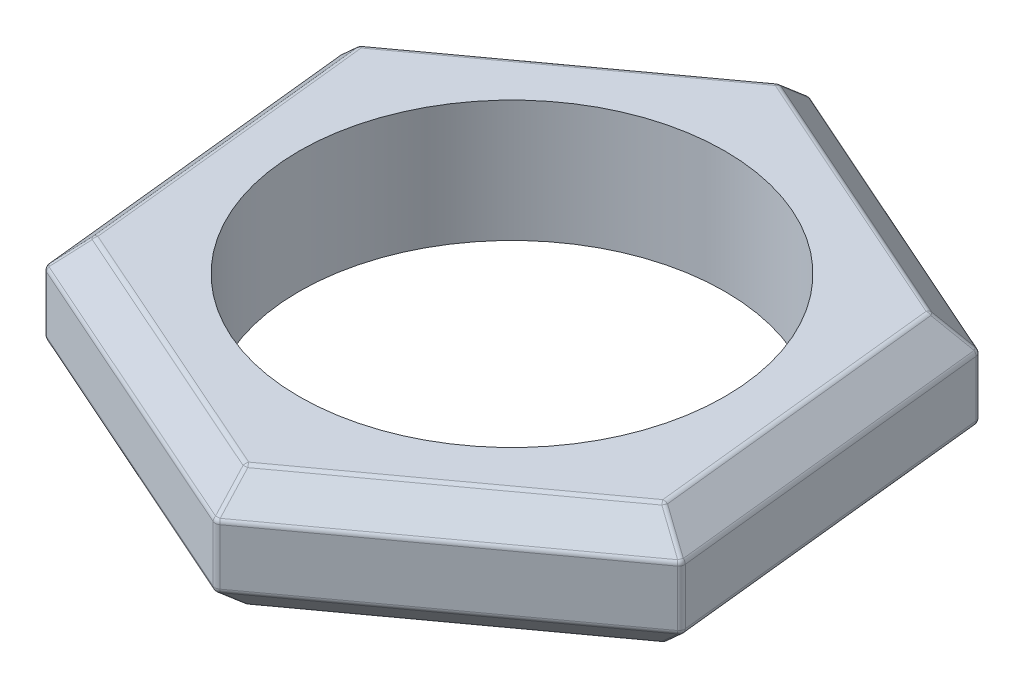
SolidWorks part; units mm, degrees
ref_plane "Front" through (0, 0, 0) normal (0, 0, 1) x (1, 0, 0)
ref_plane "Top" through (0, 0, 0) normal (0, 1, 0) x (1, 0, 0)
ref_plane "Right" through (0, 0, 0) normal (1, 0, 0) x (0, 0, -1)
sketch "Sketch1" plane through (0, 0, 0) normal (0, 1, 0) x (1, 0, 0)
  line L1 (5.028, -2.2293) -> (4.4446, 3.2397)
  line L2 (4.4446, 3.2397) -> (-0.5834, 5.469)
  line L3 (-0.5834, 5.469) -> (-5.028, 2.2293)
  line L4 (-5.028, 2.2293) -> (-4.4446, -3.2397)
  line L5 (-4.4446, -3.2397) -> (0.5834, -5.469)
  line L6 (0.5834, -5.469) -> (5.028, -2.2293)
  circle A0 centre (0, 0) radius 3.5
extrude "Extrude1" add sketch "Sketch1" along normal blind 2
chamfer "Chamfer1" distance 0.5 angle 45 6 edges at (-1.9306, 2, 4.3543) (-4.7363, 2, 0.5052) (-2.8057, 2, -3.8491) (1.9306, 2, -4.3543) (4.7363, 2, -0.5052) (2.8057, 2, 3.8491)
chamfer "Chamfer2" distance 0.5 angle 45 6 edges at (-4.7363, 0, 0.5052) (-2.8057, 0, -3.8491) (1.9306, 0, -4.3543) (4.7363, 0, -0.5052) (2.8057, 0, 3.8491) (-1.9306, 0, 4.3543)
fillet "Fillet1" radius 0.1 42 edges at (2.5111, 2, 3.4451) (2.8057, 1.5, 3.8491) (0.5834, 1, 5.469) (0.5527, 1.75, 5.1819) (-1.728, 2, 3.8972) (-1.9306, 1.5, 4.3543) (-4.4446, 1, 3.2397) (-4.2113, 1.75, 3.0697) (-4.7363, 1.5, 0.5052) (-4.2391, 2, 0.4522) (-4.7641, 1.75, -2.1123) (-5.028, 1, -2.2293) (-2.5111, 2, -3.4451) (-2.8057, 1.5, -3.8491) (-0.5527, 1.75, -5.1819) (-0.5834, 1, -5.469) (1.728, 2, -3.8972) (1.9306, 1.5, -4.3543) (4.2391, 2, -0.4522) (4.2113, 1.75, -3.0697) (4.4446, 1, -3.2397) (5.028, 1, 2.2293) (4.7641, 1.75, 2.1123) (4.7363, 1.5, -0.5052) (-0.5527, 0.25, -5.1819) (4.2113, 0.25, -3.0697) (4.7641, 0.25, 2.1123) (0.5527, 0.25, 5.1819) (-4.7641, 0.25, -2.1123) (-4.2113, 0.25, 3.0697) (-4.7363, 0.5, 0.5052) (-4.2391, 0, 0.4522) (-2.8057, 0.5, -3.8491) (-2.5111, 0, -3.4451) (1.9306, 0.5, -4.3543) (1.728, 0, -3.8972) (4.7363, 0.5, -0.5052) (4.2391, 0, -0.4522) (2.8057, 0.5, 3.8491) (2.5111, 0, 3.4451) (-1.9306, 0.5, 4.3543) (-1.728, 0, 3.8972)
